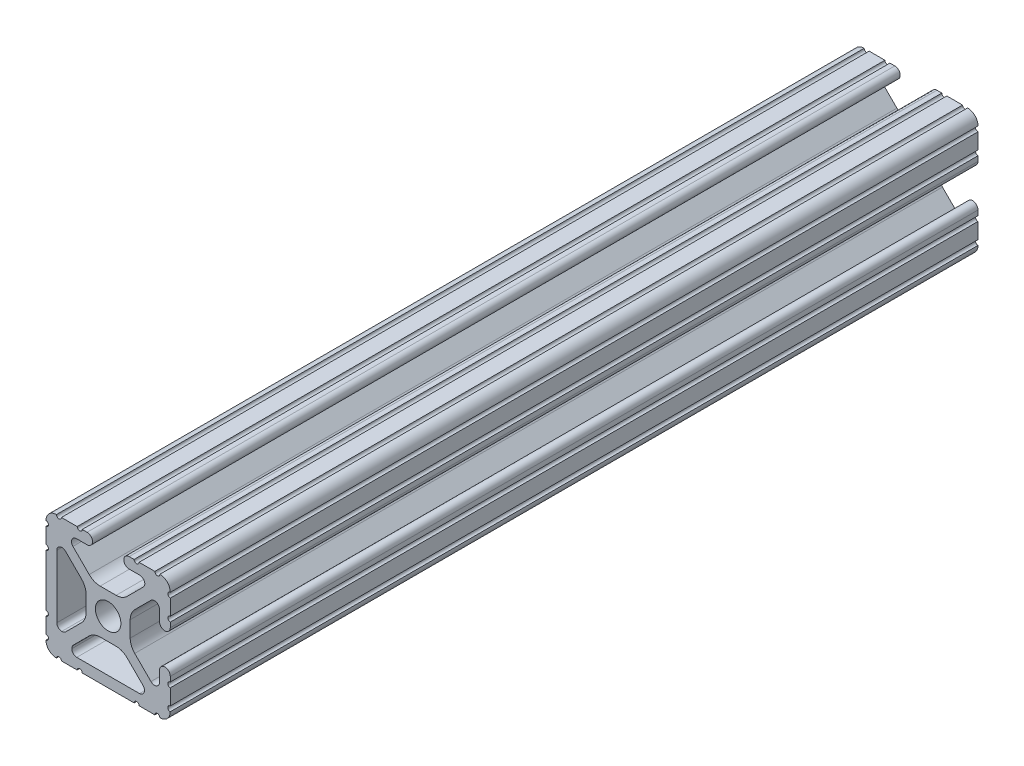
SolidWorks part; units mm, degrees
ref_plane "Front Plane" through (0, 0, 0) normal (0, 0, 1) x (1, 0, 0)
ref_plane "Top Plane" through (0, 0, 0) normal (0, 1, 0) x (1, 0, 0)
ref_plane "Right Plane" through (0, 0, 0) normal (1, 0, 0) x (0, 0, -1)
ref_plane "Plane1" through (0, 0, -558.8) normal (0, 0, -1) x (-1, 0, 0)
sketch "Sketch1" plane through (0, 0, -558.8) normal (0, 0, -1) x (-1, 0, 0)
  line L0 (12.7, -9.5504) -> (12.7, -6.3246)
  line L1 (12.7, -5.3086) -> (12.7, 5.3086)
  line L2 (12.7, 6.3246) -> (12.7, 9.5504)
  line L3 (9.5504, 12.7) -> (6.3246, 12.7)
  line L4 (5.3086, 12.7) -> (4.3023, 12.7)
  line L5 (4.3023, 10.4902) -> (6.4748, 10.4902)
  line L6 (7.1932, 8.7558) -> (3.8759, 5.4384)
  line L7 (1.6308, 4.5085) -> (-1.6308, 4.5085)
  line L8 (-3.8759, 5.4384) -> (-7.1932, 8.7558)
  line L9 (-6.4748, 10.4902) -> (-4.3023, 10.4902)
  line L10 (-4.3023, 12.7) -> (-5.3086, 12.7)
  line L11 (-6.3246, 12.7) -> (-9.5504, 12.7)
  line L12 (-12.7, 9.5504) -> (-12.7, 6.3246)
  line L13 (-12.7, 5.3086) -> (-12.7, 4.3023)
  line L14 (-10.4902, 4.3023) -> (-10.4902, 6.4748)
  line L15 (-8.7558, 7.1932) -> (-5.4384, 3.8759)
  line L16 (-4.5085, 1.6308) -> (-4.5085, -1.6308)
  line L17 (-5.4384, -3.8759) -> (-8.7558, -7.1932)
  line L18 (-10.4902, -6.4748) -> (-10.4902, -4.3023)
  line L19 (-12.7, -4.3023) -> (-12.7, -5.3086)
  line L20 (-12.7, -6.3246) -> (-12.7, -9.5504)
  line L21 (-9.5504, -12.7) -> (-6.3246, -12.7)
  line L22 (-5.3086, -12.7) -> (5.3086, -12.7)
  line L23 (6.3246, -12.7) -> (9.5504, -12.7)
  line L24 (3.8759, -5.4384) -> (7.1319, -8.6945)
  line L25 (6.4135, -10.4902) -> (-6.4135, -10.4902)
  line L26 (-7.1319, -8.6945) -> (-3.8759, -5.4384)
  line L27 (-1.6308, -4.5085) -> (1.6308, -4.5085)
  line L28 (10.4902, 6.4135) -> (10.4902, -6.4135)
  line L29 (8.6945, -7.1319) -> (5.4384, -3.8759)
  line L30 (4.5085, -1.6308) -> (4.5085, 1.6308)
  line L31 (5.4384, 3.8759) -> (8.6945, 7.1319)
  arc A0 (12.7, -10.5664) -> (12.7, -9.5504) centre (12.7, -10.0584) cw
  arc A1 (12.7, -6.3246) -> (12.7, -5.3086) centre (12.7, -5.8166) cw
  arc A2 (12.7, 5.3086) -> (12.7, 6.3246) centre (12.7, 5.8166) cw
  arc A3 (12.7, 9.5504) -> (12.7, 10.5664) centre (12.7, 10.0584) cw
  arc A4 (12.7, 10.5664) -> (10.5664, 12.7) centre (10.592, 10.592) ccw
  arc A5 (10.5664, 12.7) -> (9.5504, 12.7) centre (10.0584, 12.7) cw
  arc A6 (6.3246, 12.7) -> (5.3086, 12.7) centre (5.8166, 12.7) cw
  arc A7 (4.3023, 12.7) -> (4.3023, 10.4902) centre (4.3023, 11.5951) ccw
  arc A8 (6.4748, 10.4902) -> (7.1932, 8.7558) centre (6.4748, 9.4742) cw
  arc A9 (3.8759, 5.4384) -> (1.6308, 4.5085) centre (1.6308, 7.6835) cw
  arc A10 (-1.6308, 4.5085) -> (-3.8759, 5.4384) centre (-1.6308, 7.6835) cw
  arc A11 (-7.1932, 8.7558) -> (-6.4748, 10.4902) centre (-6.4748, 9.4742) cw
  arc A12 (-4.3023, 10.4902) -> (-4.3023, 12.7) centre (-4.3023, 11.5951) ccw
  arc A13 (-5.3086, 12.7) -> (-6.3246, 12.7) centre (-5.8166, 12.7) cw
  arc A14 (-9.5504, 12.7) -> (-10.5664, 12.7) centre (-10.0584, 12.7) cw
  arc A15 (-10.5664, 12.7) -> (-12.7, 10.5664) centre (-10.592, 10.592) ccw
  arc A16 (-12.7, 10.5664) -> (-12.7, 9.5504) centre (-12.7, 10.0584) cw
  arc A17 (-12.7, 6.3246) -> (-12.7, 5.3086) centre (-12.7, 5.8166) cw
  arc A18 (-12.7, 4.3023) -> (-10.4902, 4.3023) centre (-11.5951, 4.3023) ccw
  arc A19 (-10.4902, 6.4748) -> (-8.7558, 7.1932) centre (-9.4742, 6.4748) cw
  arc A20 (-5.4384, 3.8759) -> (-4.5085, 1.6308) centre (-7.6835, 1.6308) cw
  arc A21 (-4.5085, -1.6308) -> (-5.4384, -3.8759) centre (-7.6835, -1.6308) cw
  arc A22 (-8.7558, -7.1932) -> (-10.4902, -6.4748) centre (-9.4742, -6.4748) cw
  arc A23 (-10.4902, -4.3023) -> (-12.7, -4.3023) centre (-11.5951, -4.3023) ccw
  arc A24 (-12.7, -5.3086) -> (-12.7, -6.3246) centre (-12.7, -5.8166) cw
  arc A25 (-12.7, -9.5504) -> (-12.7, -10.5664) centre (-12.7, -10.0584) cw
  arc A26 (-12.7, -10.5664) -> (-10.5664, -12.7) centre (-10.592, -10.592) ccw
  arc A27 (-10.5664, -12.7) -> (-9.5504, -12.7) centre (-10.0584, -12.7) cw
  arc A28 (-6.3246, -12.7) -> (-5.3086, -12.7) centre (-5.8166, -12.7) cw
  arc A29 (5.3086, -12.7) -> (6.3246, -12.7) centre (5.8166, -12.7) cw
  arc A30 (9.5504, -12.7) -> (10.5664, -12.7) centre (10.0584, -12.7) cw
  arc A31 (10.5664, -12.7) -> (12.7, -10.5664) centre (10.592, -10.592) ccw
  circle A32 centre (0, 0) radius 2.6035
  arc A33 (7.1319, -8.6945) -> (7.4295, -9.4742) centre (6.2865, -9.4638) cw
  arc A34 (7.4295, -9.4742) -> (6.4135, -10.4902) centre (6.4135, -9.4742) cw
  arc A35 (-6.4135, -10.4902) -> (-7.4295, -9.4742) centre (-6.4135, -9.4742) cw
  arc A36 (-7.4295, -9.4742) -> (-7.1319, -8.6945) centre (-6.2865, -9.4638) cw
  arc A37 (-3.8759, -5.4384) -> (-1.6308, -4.5085) centre (-1.6308, -7.6835) cw
  arc A38 (1.6308, -4.5085) -> (3.8759, -5.4384) centre (1.6308, -7.6835) cw
  arc A39 (9.4742, 7.4295) -> (10.4902, 6.4135) centre (9.4742, 6.4135) cw
  arc A40 (10.4902, -6.4135) -> (9.4742, -7.4295) centre (9.4742, -6.4135) cw
  arc A41 (9.4742, -7.4295) -> (8.6945, -7.1319) centre (9.4638, -6.2865) cw
  arc A42 (5.4384, -3.8759) -> (4.5085, -1.6308) centre (7.6835, -1.6308) cw
  arc A43 (4.5085, 1.6308) -> (5.4384, 3.8759) centre (7.6835, 1.6308) cw
  arc A44 (8.6945, 7.1319) -> (9.4742, 7.4295) centre (9.4638, 6.2865) cw
extrude "Boss-Extrude1" add sketch "Sketch1" against normal blind 165.1
